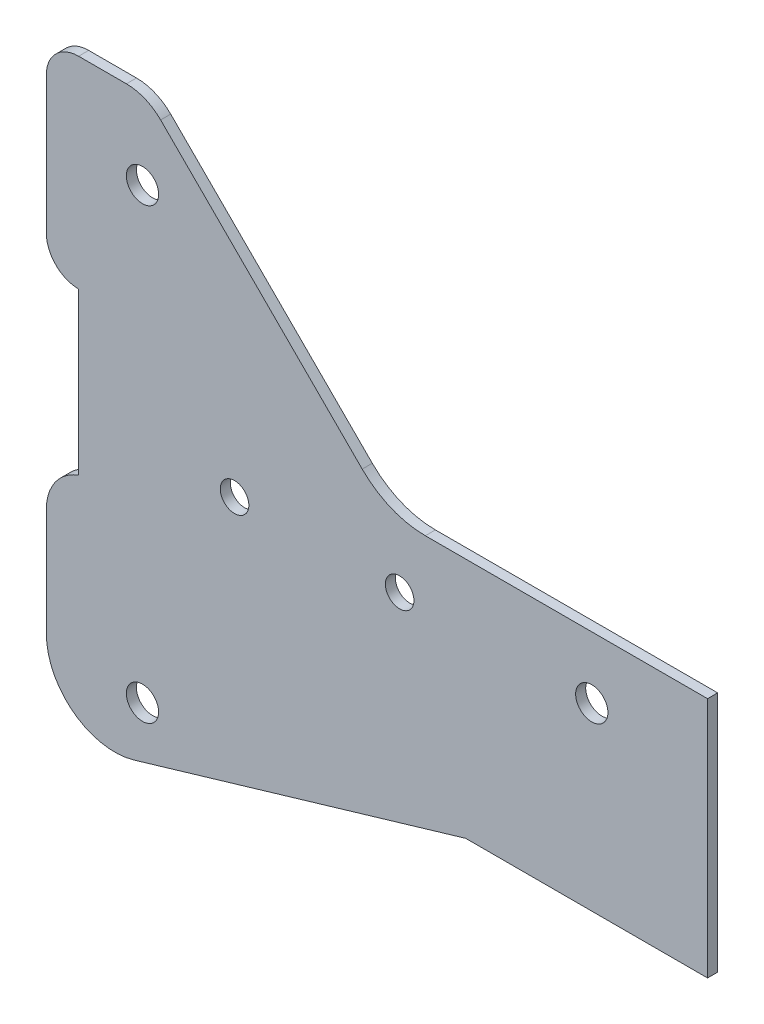
SolidWorks part; units mm, degrees
ref_plane "Front Plane" through (0, 0, 0) normal (0, 0, 1) x (1, 0, 0)
ref_plane "Top Plane" through (0, 0, 0) normal (0, 1, 0) x (1, 0, 0)
ref_plane "Right Plane" through (0, 0, 0) normal (1, 0, 0) x (0, 0, -1)
sketch "Sketch1" plane through (0, 0, 0) normal (0, 0, 1) x (1, 0, 0)
  line L0 (0, 0) -> (-44.45, 0)
  line L5 (0, 0) -> (0, -38.1)
  line L6 (0, -38.1) -> (-38.1, -38.1)
  line L7 (-54.3921, 4.1182) -> (-86.1421, 35.8682)
  line L8 (-93.3643, -43.1993) -> (-93.3643, -53.975) construction
  line L9 (-104.14, 33.02) -> (-104.14, 11.43)
  line L11 (-99.06, 38.1) -> (-91.5303, 38.1)
  line L12 (-99.06, 6.35) -> (-99.06, -19.05)
  line L13 (-104.14, -26.2342) -> (-104.14, -43.1993)
  line L14 (-89, 25.555) -> (-89, -45.055) construction
  line L15 (-99.06, 11.43) -> (-99.06, 6.35) construction
  line L16 (-38.1, -38.1) -> (-90.3097, -53.533)
  line L17 (-89, -9.75) -> (-18.24, -9.75) construction
  arc A0 (-54.3921, 4.1182) -> (-44.45, 0) centre (-44.45, 14.0603) ccw
  arc A8 (-99.06, 38.1) -> (-104.14, 33.02) centre (-99.06, 33.02) ccw
  arc A9 (-91.5303, 38.1) -> (-86.1421, 35.8682) centre (-91.5303, 30.48) cw
  arc A10 (-99.06, -19.05) -> (-104.14, -26.2342) centre (-96.52, -26.2342) ccw
  arc A11 (-104.14, 11.43) -> (-99.06, 6.35) centre (-99.06, 11.43) ccw
  arc A12 (-104.14, -43.1993) -> (-90.3097, -53.533) centre (-93.3643, -43.1993) ccw
  circle A13 centre (-89, 25.555) radius 2.54
  circle A14 centre (-89, -45.055) radius 2.54
  circle A15 centre (-18.24, -9.75) radius 2.54
  circle A16 centre (-74.5, -9.75) radius 2.25
  circle A17 centre (-48.5, -9.75) radius 2.25
  dimension "D3" = 135
  dimension "D6" = 38.1
  dimension "D7" = 5.08
  dimension "D8" = 7.62
  dimension "D10" = 38.1
  dimension "D12" = 7.62
  dimension "D9" = 5.08
  dimension "D20" = 4.5
  dimension "D21" = 4.5
  dimension "D1" = 38.1
  dimension "D2" = 44.45
  dimension "D4" = 104.14
  dimension "D5" = 92.075
  dimension "D11" = 163.533
  dimension "D13" = 31.75
  dimension "D14" = 6.35
  dimension "D15" = 25.4
  dimension "D16" = 70.76
  dimension "D17" = 70.61
  dimension "D18" = 89
  dimension "D19" = 9.75
  dimension "D22" = 56.26
  dimension "D23" = 26
extrude "Boss-Extrude1" add sketch "Sketch1" along normal blind 1.5875
